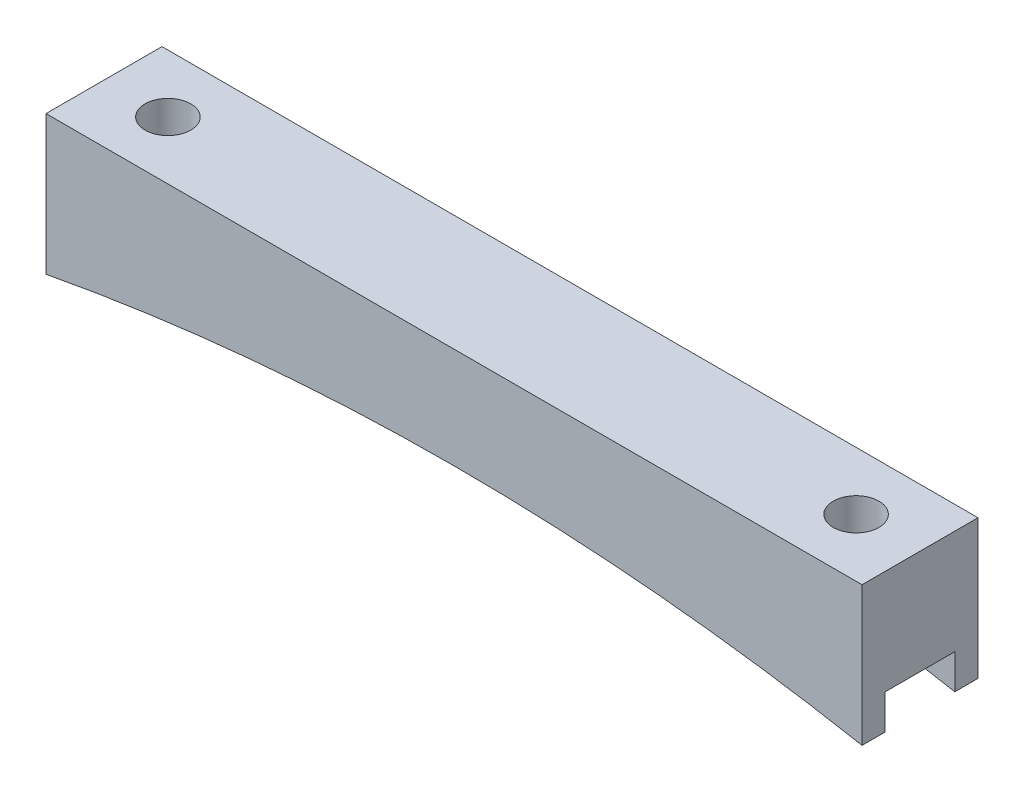
SolidWorks part; units mm, degrees
ref_plane "Front Plane" through (0, 0, 0) normal (0, 0, 1) x (1, 0, 0)
ref_plane "Top Plane" through (0, 0, 0) normal (0, 1, 0) x (1, 0, 0)
ref_plane "Right Plane" through (0, 0, 0) normal (1, 0, 0) x (0, 0, -1)
sketch "Sketch1" plane through (0, 0, 0) normal (0, 0, 1) x (1, 0, 0)
  line L0 (-44.68, 0) -> (44.68, 0)
  line L1 (-37.68, -2.54) -> (37.68, -2.54) construction
  line L2 (0, 0) -> (0, -4.6068) construction
  line L3 (44.68, 0) -> (44.68, -15.24)
  line L4 (-44.68, 0) -> (-44.68, -15.24)
  arc A0 (-44.68, -15.24) -> (44.68, -15.24) centre (0, -252.3674) cw
  point P4 (0, 0)
  point P9 (0, -2.54)
  dimension "D4" = 241.3
  dimension "D1" = 75.36
  dimension "D2" = 2.54
  dimension "D3" = 7
  dimension "D5" = 15.24
extrude "Boss-Extrude1" add sketch "Sketch1" along normal blind 12.7
sketch "Sketch2" plane through (0, 0, 0) normal (0, 1, 0) x (1, 0, 0)
  line L1 (-37.68, 0) -> (-37.68, -12.7) construction
  line L2 (-44.68, 0) -> (44.68, 0) construction
  line L3 (44.68, -12.7) -> (-44.68, -12.7) construction
  line L4 (37.68, 0) -> (37.68, -12.7) construction
  circle A0 centre (-37.68, -6.35) radius 2.5
  circle A1 centre (37.68, -6.35) radius 2.5
  circle A2 centre (-37.68, -6.35) radius 3 construction
  point P7 (-37.68, -6.35)
  dimension "D1" = 5
  dimension "D2" = 6
extrude "Cut-Extrude1" cut sketch "Sketch2" against normal through all
sketch "Sketch3" plane through (44.68, 0, 0) normal (1, 0, 0) x (0, 0, -1)
  line L0 (-12.7, -15.24) -> (0, -15.24) construction
  line L1 (-10.16, -15.24) -> (-2.54, -15.24)
  line L2 (-10.16, -15.24) -> (-10.16, -11.43)
  line L3 (-10.16, -11.43) -> (-2.54, -11.43)
  line L4 (-2.54, -15.24) -> (-2.54, -11.43)
  line L5 (-12.7, -15.24) -> (-12.7, 0) construction
  line L6 (0, -15.24) -> (0, 0) construction
  dimension "D1" = 2.54
  dimension "D2" = 2.54
  dimension "D3" = 3.81
extrude "Cut-Extrude2" cut sketch "Sketch3" against normal through all
